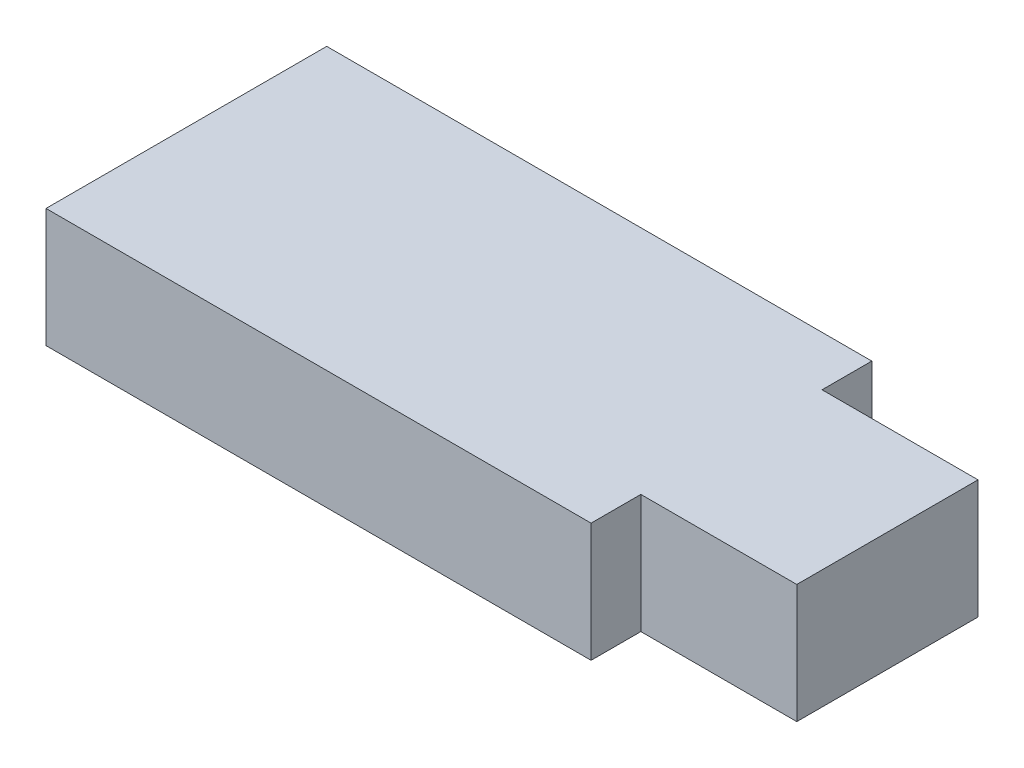
SolidWorks part; units mm, degrees
ref_plane "Front Plane" through (0, 0, 0) normal (0, 0, 1) x (1, 0, 0)
ref_plane "Top Plane" through (0, 0, 0) normal (0, 1, 0) x (1, 0, 0)
ref_plane "Right Plane" through (0, 0, 0) normal (1, 0, 0) x (0, 0, -1)
sketch "Sketch1" plane through (0, 0, 0) normal (0, 1, 0) x (1, 0, 0)
  line L0 (0, 0) -> (0, 18.9)
  line L1 (0, 18.9) -> (36.7, 18.9)
  line L2 (36.7, 18.9) -> (36.7, 15.55)
  line L3 (36.7, 15.55) -> (47.2, 15.55)
  line L4 (47.2, 15.55) -> (47.2, 3.35)
  line L5 (47.2, 3.35) -> (36.7, 3.35)
  line L6 (36.7, 3.35) -> (36.7, 0)
  line L7 (36.7, 0) -> (0, 0)
  dimension "D1" = 36.7
  dimension "D2" = 18.9
  dimension "D3" = 12.2
  dimension "D4" = 10.5
extrude "Boss-Extrude1" add sketch "Sketch1" along normal blind 8
